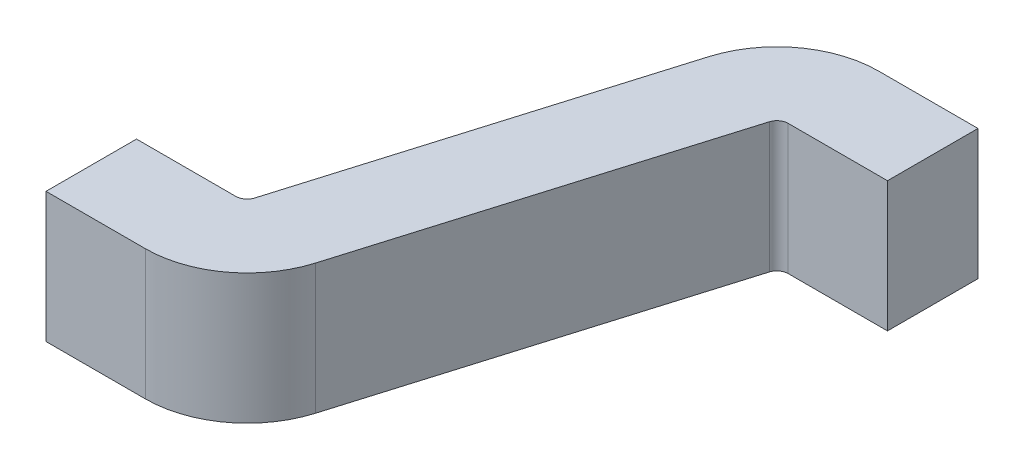
SolidWorks part; units mm, degrees
ref_plane "Front Plane" through (0, 0, 0) normal (0, 0, 1) x (1, 0, 0)
ref_plane "Top Plane" through (0, 0, 0) normal (0, 1, 0) x (1, 0, 0)
ref_plane "Right Plane" through (0, 0, 0) normal (1, 0, 0) x (0, 0, -1)
sketch "Sketch1" plane through (0, 0, 0) normal (0, 1, 0) x (1, 0, 0)
  line L0 (0, 0) -> (0.3511, 0) construction
  line L1 (0.5427, 0.1426) -> (0.9123, 1.3774) construction
  line L2 (1.1039, 1.52) -> (1.455, 1.52) construction
  line L3 (0, -0.16) -> (0.3511, -0.16)
  line L4 (0.696, 0.0968) -> (1.0656, 1.3315)
  line L5 (1.1039, 1.36) -> (1.455, 1.36)
  line L6 (0, 0.16) -> (0.3511, 0.16)
  line L7 (0.3894, 0.1885) -> (0.759, 1.4232)
  line L8 (1.1039, 1.68) -> (1.455, 1.68)
  line L9 (0, -0.16) -> (0, 0.16)
  line L10 (1.455, 1.36) -> (1.455, 1.68)
  arc A0 (0.9123, 1.3774) -> (1.1039, 1.52) centre (1.1039, 1.32) cw construction
  arc A1 (0.3511, 0) -> (0.5427, 0.1426) centre (0.3511, 0.2) ccw construction
  arc A2 (0.3511, -0.16) -> (0.696, 0.0968) centre (0.3511, 0.2) ccw
  arc A3 (1.0656, 1.3315) -> (1.1039, 1.36) centre (1.1039, 1.32) cw
  arc A4 (0.3511, 0.16) -> (0.3894, 0.1885) centre (0.3511, 0.2) ccw
  arc A5 (0.759, 1.4232) -> (1.1039, 1.68) centre (1.1039, 1.32) cw
  point P6 (0.955, 1.52)
  point P9 (1.2794, 1.52)
  dimension "D4" = 0.2
  dimension "D1" = 1.455
  dimension "D2" = 0.5
  dimension "D3" = 1.52
  dimension "D5" = 0.16
  dimension "D6" = 0.16
extrude "Boss-Extrude1" add sketch "Sketch1" along normal mid plane 0.46
